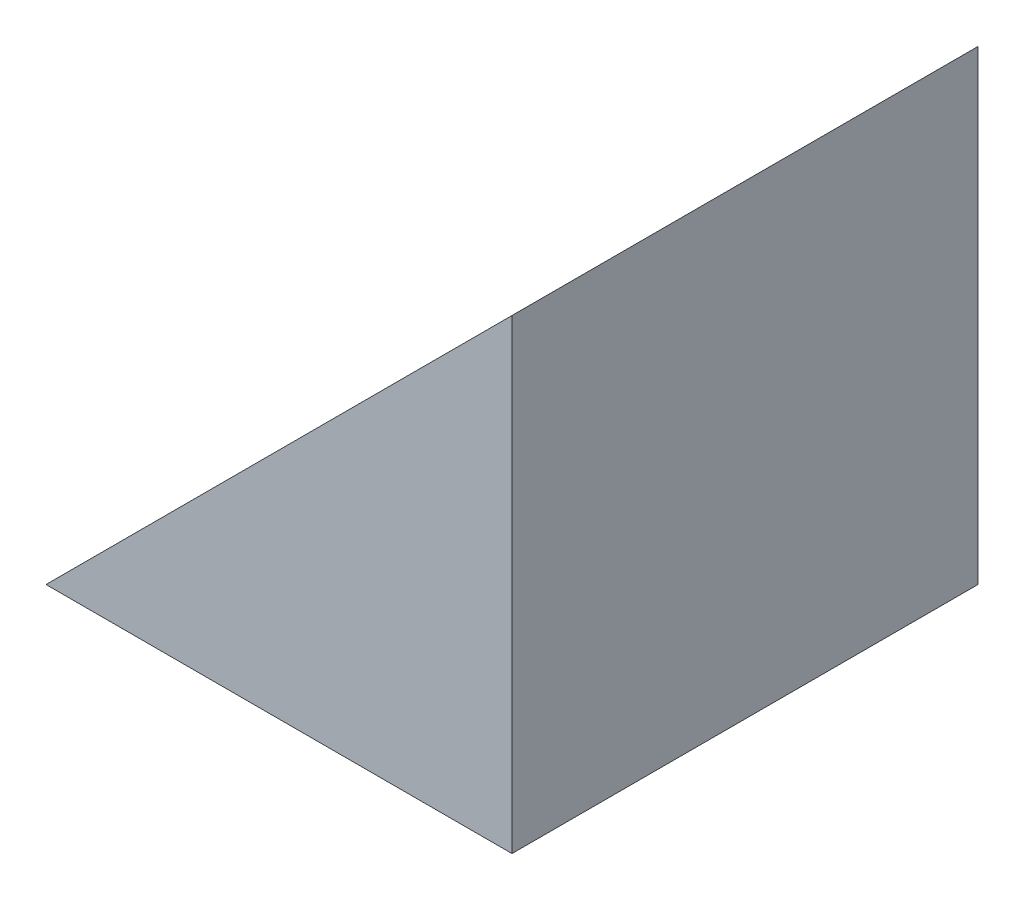
SolidWorks part; units mm, degrees
ref_plane "前视基准面" through (0, 0, 0) normal (0, 0, 1) x (1, 0, 0)
ref_plane "上视基准面" through (0, 0, 0) normal (0, 1, 0) x (1, 0, 0)
ref_plane "右视基准面" through (0, 0, 0) normal (1, 0, 0) x (0, 0, -1)
sketch "草图1" plane through (0, 0, 0) normal (0, 0, 1) x (1, 0, 0)
  line L0 (22.014, 16.7302) -> (22.014, 23.0302)
  line L1 (22.014, 16.7302) -> (15.714, 16.7302)
  line L2 (15.714, 16.7302) -> (22.014, 23.0302)
  dimension "D1" = 6.3
  dimension "D2" = 6.3
extrude "凸台-拉伸1" add sketch "草图1" along normal blind 6.3
